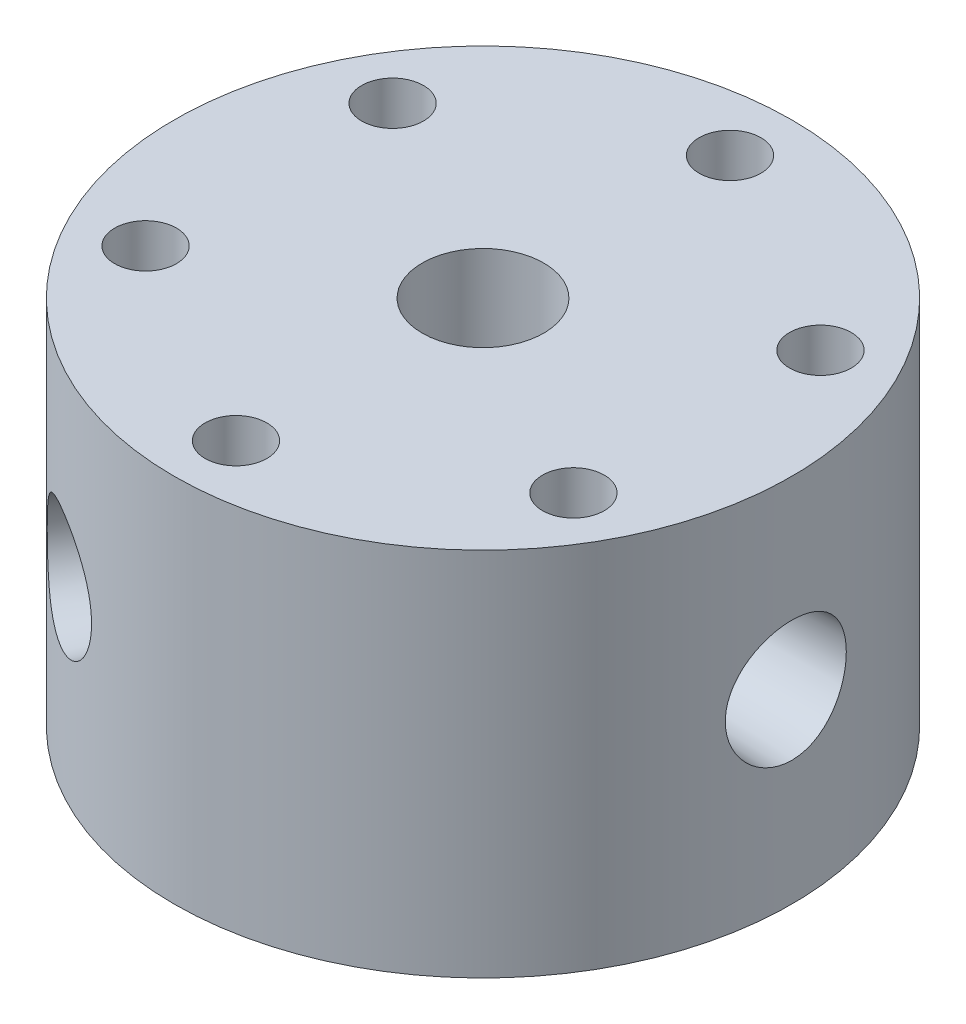
SolidWorks part; units mm, degrees
ref_plane "Front Plane" through (0, 0, 0) normal (0, 0, 1) x (1, 0, 0)
ref_plane "Top Plane" through (0, 0, 0) normal (0, 1, 0) x (1, 0, 0)
ref_plane "Right Plane" through (0, 0, 0) normal (1, 0, 0) x (0, 0, -1)
sketch "Sketch1" plane through (0, 0, 0) normal (0, 0, 1) x (1, 0, 0)
  line L2 (-6.35, 0) -> (-31.75, 0)
  line L3 (-31.75, 0) -> (-31.75, 38.1)
  line L4 (-31.75, 38.1) -> (-3.81, 38.1)
  line L6 (-3.81, 38.1) -> (-3.81, 6.35)
  line L10 (0, 0) -> (0, 15.7692) construction
  line L11 (-3.81, 6.35) -> (-6.35, 6.35)
  line L12 (-6.35, 6.35) -> (-6.35, 0)
  dimension "D1" = 3.81
  dimension "D2" = 6.35
  dimension "D3" = 6.35
  dimension "D4" = 38.1
  dimension "D5" = 31.75
revolve "Revolve1" add sketch "Sketch1" angle 360 about L10
hole_wizard "M14x1.5 Tapped Hole1" positions "Sketch2" profile "Sketch4" tap size "M14x1.5" standard "ANSI Metric"
sketch "Sketch2" plane through (0, 38.1, 0) normal (0, 1, 0) x (1, 0, 0)
  point P0 (0, 0)
sketch "Sketch4" plane through (0, 38.1, 0) normal (1, 0, 0) x (0, 0, 1)
  line L0 (0, 0) -> (0, 29.1554)
  line L1 (0, 29.1554) -> (6.25, 25.4)
  line L2 (6.25, 25.4) -> (6.25, 0)
  line L5 (6.25, 0) -> (0, 0)
  line L10 (0, 29.1554) -> (-6.25, 25.4) construction
  line L11 (0, -6.35) -> (0, 107.95) construction
  dimension "Tap Drill Dia." = 12.5
  dimension "Tap Drill Depth" = 25.4
  dimension "Drill Angle" = 118
cosmetic thread "Hole Thread3"
ref_plane "Plane1" through (31.75, 0, 0) normal (1, 0, 0) x (0, 0, -1)
ref_plane "Plane2" through (-31.75, 0, 0) normal (-1, 0, 0) x (0, 0, 1)
hole_wizard "1/4 NPT Tapped Hole1" positions "Sketch5" profile "Sketch6" size "1/4" standard "ANSI Inch"
sketch "Sketch5" plane through (31.75, 0, 0) normal (1, 0, 0) x (0, 0, -1)
  line L0 (31.75, 38.1) -> (-31.75, 38.1) construction
  point P0 (0, 19.05)
  dimension "D1" = 19.05
sketch "Sketch6" plane through (31.75, 19.05, 0) normal (0, 1, 0) x (0, 0, -1)
  line L0 (0, 0) -> (0, 20.3603)
  line L1 (5.5626, 17.018) -> (0, 20.3603)
  line L2 (-5.5626, 17.018) -> (0, 20.3603) construction
  line L3 (5.5626, 17.018) -> (5.5626, 9.906)
  line L4 (5.5626, 9.906) -> (5.9437, 9.906)
  line L5 (5.9437, 9.906) -> (6.2403, 0)
  line L6 (-5.9437, 9.906) -> (-6.2403, 0) construction
  line L7 (6.2403, 0) -> (0, 0)
  line L8 (0, -6.35) -> (0, 107.95) construction
  line L11 (-5.5626, 9.906) -> (-5.9437, 9.906) construction
  dimension "Tap Drill Dia." = 11.1252
  dimension "Tap Drill Depth" = 17.018
  dimension "Thread Dia." = 12.4806
  dimension "Thread Angle" = 3.43
  dimension "Thread Depth" = 9.906
  dimension "Drill Angle" = 118
cosmetic thread "Hole Thread1"
hole_wizard "1/4 NPT Tapped Hole2" positions "Sketch7" profile "Sketch8" size "1/4" standard "ANSI Inch"
sketch "Sketch7" plane through (-31.75, 0, 0) normal (-1, 0, 0) x (0, 0, 1)
  line L0 (31.75, 38.1) -> (-31.75, 38.1) construction
  point P0 (0, 19.05)
  dimension "D1" = 19.05
sketch "Sketch8" plane through (-31.75, 19.05, 0) normal (0, 1, 0) x (0, 0, 1)
  line L0 (0, 0) -> (0, 20.3603)
  line L1 (5.5626, 17.018) -> (0, 20.3603)
  line L2 (-5.5626, 17.018) -> (0, 20.3603) construction
  line L3 (5.5626, 17.018) -> (5.5626, 9.906)
  line L4 (5.5626, 9.906) -> (5.9437, 9.906)
  line L5 (5.9437, 9.906) -> (6.2403, 0)
  line L6 (-5.9437, 9.906) -> (-6.2403, 0) construction
  line L7 (6.2403, 0) -> (0, 0)
  line L8 (0, -6.35) -> (0, 107.95) construction
  line L11 (-5.5626, 9.906) -> (-5.9437, 9.906) construction
  dimension "Tap Drill Dia." = 11.1252
  dimension "Tap Drill Depth" = 17.018
  dimension "Thread Dia." = 12.4806
  dimension "Thread Angle" = 3.43
  dimension "Thread Depth" = 9.906
  dimension "Drill Angle" = 118
cosmetic thread "Hole Thread2" parameters "D1"=9.906, "D2"=13.7086
hole_wizard "1/16 (0.0625) Diameter Hole1" positions "Sketch9" profile "Sketch10" hole size "1/16" standard "ANSI Inch"
sketch "Sketch9" plane through (31.75, 0, 0) normal (1, 0, 0) x (0, 0, -1)
  point P0 (0, 19.05)
sketch "Sketch10" plane through (31.75, 19.05, 0) normal (0, 1, 0) x (0, 0, -1)
  line L0 (0, 0) -> (0, 29.0519)
  line L1 (0, 29.0519) -> (0.7937, 28.575)
  line L2 (0.7937, 28.575) -> (0.7937, 0)
  line L5 (0.7937, 0) -> (0, 0)
  line L10 (0, 29.0519) -> (-0.7938, 28.575) construction
  line L11 (0, -6.35) -> (0, 107.95) construction
  dimension "Hole Dia." = 1.5875
  dimension "Hole Depth" = 28.575
  dimension "Drill Angle" = 118
hole_wizard "3/32 (0.09375) Diameter Hole1" positions "Sketch11" profile "Sketch12" hole size "3/32" standard "ANSI Inch"
sketch "Sketch11" plane through (-31.75, 0, 0) normal (-1, 0, 0) x (0, 0, 1)
  point P0 (0, 19.05)
sketch "Sketch12" plane through (-31.75, 19.05, 0) normal (0, 1, 0) x (0, 0, 1)
  line L0 (0, 0) -> (0, 29.4174)
  line L1 (0, 29.4174) -> (1.1906, 28.702)
  line L2 (1.1906, 28.702) -> (1.1906, 0)
  line L5 (1.1906, 0) -> (0, 0)
  line L10 (0, 29.4174) -> (-1.1906, 28.702) construction
  line L11 (0, -6.35) -> (0, 107.95) construction
  dimension "Hole Dia." = 2.3812
  dimension "Hole Depth" = 28.702
  dimension "Drill Angle" = 118
hole_wizard "1/4 (0.25) Diameter Hole1" positions "Sketch15" profile "Sketch16" hole size "1/4" standard "ANSI Inch" end condition through all
sketch "Sketch15" plane through (0, 38.1, 0) normal (0, 1, 0) x (1, 0, 0)
  line L0 (0, 0) -> (16.0984, 0) construction
  line L2 (0, 0) -> (21.997, 12.7) construction
  point P0 (21.997, 12.7)
  dimension "D1" = 25.4
  dimension "D2" = 30
sketch "Sketch16" plane through (21.997, 38.1, -12.7) normal (1, 0, 0) x (0, 0, 1)
  line L0 (0, 0) -> (0, 38.1)
  line L1 (0, 38.1) -> (3.175, 38.1)
  line L2 (3.175, 38.1) -> (3.175, 0)
  line L5 (3.175, 0) -> (0, 0)
  line L11 (0, -6.35) -> (0, 107.95) construction
  dimension "Thru Hole Dia." = 6.35
  dimension "Thru Hole Depth" = 38.1
pattern_circular "CirPattern1" count 6 over 360 about axis through (0, 0, 0) along (0, 1, 0) of "1/4 (0.25) Diameter Hole1"
ref_plane "Plane3" through (-15.875, 0, 27.4963) normal (-0.5, 0, 0.866) x (0, -1, 0)
hole_wizard "1/4 NPT Tapped Hole3" positions "Sketch17" profile "Sketch18" size "1/4" standard "ANSI Inch"
sketch "Sketch17" plane through (-15.875, 0, 27.4963) normal (-0.5, 0, 0.866) x (0, -1, 0)
  point P0 (-19.05, 0)
  dimension "D1" = 19.05
sketch "Sketch18" plane through (-15.875, 19.05, 27.4963) normal (0, 1, 0) x (0.866, 0, 0.5)
  line L0 (0, 0) -> (0, 19.3443)
  line L1 (5.5626, 16.002) -> (0, 19.3443)
  line L2 (-5.5626, 16.002) -> (0, 19.3443) construction
  line L3 (5.5626, 16.002) -> (5.5626, 9.906)
  line L4 (5.5626, 9.906) -> (5.9437, 9.906)
  line L5 (5.9437, 9.906) -> (6.2403, 0)
  line L6 (-5.9437, 9.906) -> (-6.2403, 0) construction
  line L7 (6.2403, 0) -> (0, 0)
  line L8 (0, -6.35) -> (0, 107.95) construction
  line L11 (-5.5626, 9.906) -> (-5.9437, 9.906) construction
  dimension "Tap Drill Dia." = 11.1252
  dimension "Tap Drill Depth" = 16.002
  dimension "Thread Dia." = 12.4806
  dimension "Thread Angle" = 3.43
  dimension "Thread Depth" = 9.906
  dimension "Drill Angle" = 118
cosmetic thread "Hole Thread4"
hole_wizard "1/32 (0.03125) Diameter Hole2" positions "Sketch19" profile "Sketch20" hole size "1/32" standard "ANSI Inch"
sketch "Sketch19" plane through (-15.875, 0, 27.4963) normal (-0.5, 0, 0.866) x (0, -1, 0)
  point P0 (-19.05, 0)
sketch "Sketch20" plane through (-15.875, 19.05, 27.4963) normal (0, 1, 0) x (0.866, 0, 0.5)
  line L0 (0, 0) -> (0, 28.8135)
  line L1 (0, 28.8135) -> (0.3969, 28.575)
  line L2 (0.3969, 28.575) -> (0.3969, 0)
  line L5 (0.3969, 0) -> (0, 0)
  line L10 (0, 28.8135) -> (-0.3969, 28.575) construction
  line L11 (0, -6.35) -> (0, 107.95) construction
  dimension "Hole Dia." = 0.7937
  dimension "Hole Depth" = 28.575
  dimension "Drill Angle" = 118
